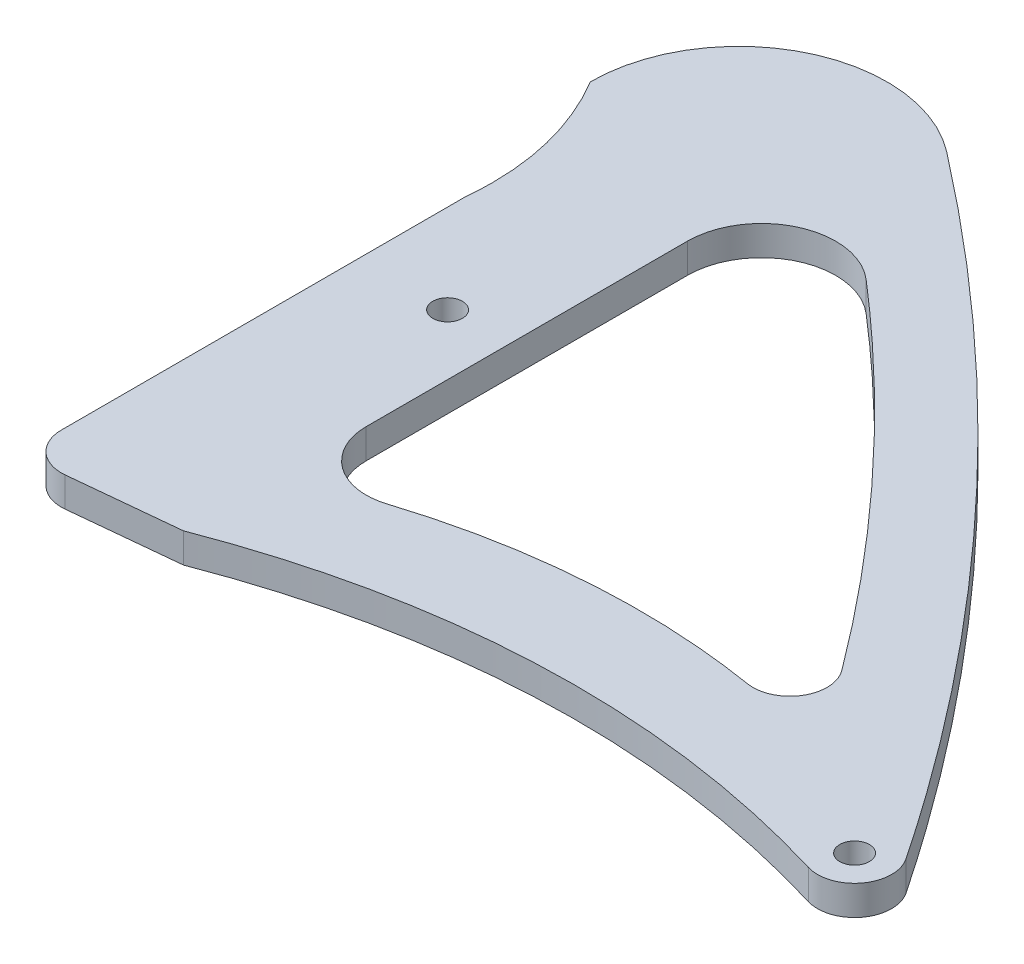
SolidWorks part; units mm, degrees
material "Hexcel AS4C (3000 Filaments)"
ref_plane "Front Plane" through (0, 0, 0) normal (0, 0, 1) x (1, 0, 0)
ref_plane "Top Plane" through (0, 0, 0) normal (0, 1, 0) x (1, 0, 0)
ref_plane "Right Plane" through (0, 0, 0) normal (1, 0, 0) x (0, 0, -1)
sketch "Sketch1" plane through (0, 0, 0) normal (0, 1, 0) x (1, 0, 0)
  line L0 (0, 0) -> (0, 40.9387)
  line L1 (0, 33.5355) -> (2.5, 33.5355) construction
  line L2 (60, 0) -> (0, 0)
  line L3 (30, 30) -> (33.5355, 33.5355) construction
  line L4 (2.5, 30) -> (2.5, 2.7625)
  line L5 (5.2488, 0.2749) -> (12.5, 1)
  line L6 (30, 0) -> (30, 5) construction
  arc A0 (0, 40.9387) -> (16.1112, 48.8541) centre (10, 40.9387) cw
  arc A1 (53.2206, 2.4136) -> (56.0179, 6.2003) centre (53.942, 4.8073) ccw
  arc A2 (5.2488, 0.2749) -> (2.5, 2.7625) centre (5, 2.7625) cw
  spline S0 degree 3 poles (16.1112, 48.8541) (22.2521, 44.1129) (36.9406, 31.1972) (49.4059, 16.0539) (56.0179, 6.2003) knots 0.227143 0.227143 0.227143 0.227143 0.499194 0.914215 0.914215 0.914215 0.914215
  spline S1 degree 2 poles (0, 40.9387) (3.0656, 35.7676) (2.5, 30) knots 0 0 0 1 1 1
  spline S2 degree 3 poles (12.5, 1) (25.7163, 6.0568) (39.5099, 6.5456) (53.2206, 2.4136) knots 0 0 0 0 0.858701 0.858701 0.858701 0.858701
  point P23 (2.5, 0)
  dimension "D1" = 10
  dimension "D2" = 2.5
  dimension "D8" = 2.5
  dimension "D3" = 5
  dimension "D4" = 2.5
  dimension "D5" = 10
  dimension "D6" = 5
  dimension "D7" = 1
extrude "Boss-Extrude1" add sketch "Sketch1" along normal blind 2 contours L5 S2 A1 S0 A0 S1 L4 A2
sketch "Sketch2" plane through (0, 2, 0) normal (0, 1, 0) x (1, 0, 0)
  line L0 (53.942, 4.8073) -> (53.942, 22.8073) construction
  line L1 (53.942, 22.8073) -> (-8.1373, 22.8073) construction
  line L2 (2.5, 30) -> (2.5, 2.7625) construction
  line L3 (36.3654, 30.6441) -> (32.8299, 27.1086) construction
  line L4 (16.1112, 48.8541) -> (12.5757, 45.3185) construction
  line L5 (12.5757, 34.9025) -> (12.5757, 13.2423)
  circle A1 centre (53.942, 4.8073) radius 1
  circle A2 centre (8.5, 22.8073) radius 1
  arc A8 (40.4375, 11.085) -> (42.8465, 15.0453) centre (40.8413, 13.5522) ccw
  arc A9 (12.5757, 34.9025) -> (20.8408, 38.6891) centre (17.5757, 34.9025) cw
  arc A10 (12.5757, 13.2423) -> (17.789, 9.4308) centre (16.5757, 13.2423) ccw
  spline S0 degree 3 poles (16.1112, 48.8541) (22.2521, 44.1129) (36.9406, 31.1972) (49.4059, 16.0539) (56.0179, 6.2003) knots 0.227143 0.227143 0.227143 0.227143 0.499194 0.914215 0.914215 0.914215 0.914215 construction
  spline S2 degree 3 poles (20.8408, 38.6891) (25.0583, 35.0525) (32.8272, 27.5467) (39.7116, 19.2551) (42.8465, 15.0453) knots 0.213221 0.213221 0.213221 0.213221 0.55034 0.867457 0.867457 0.867457 0.867457
  spline S3 degree 3 poles (40.4375, 11.085) (37.4472, 11.5745) (29.8378, 12.1103) (22.2505, 10.851) (17.789, 9.4308) knots 0.180465 0.180465 0.180465 0.180465 0.440917 0.841912 0.841912 0.841912 0.841912
  point P15 (46.6711, 9.6669)
  point P17 (12.5757, 7.4448)
  point P18 (31.4581, 11.7181)
  dimension "D1" = 18
  dimension "D2" = 6
  dimension "D5" = 5
  dimension "D4" = 2.5
  dimension "D6" = 4
  dimension "D3" = 5
extrude "Cut-Extrude1" cut sketch "Sketch2" against normal through all
